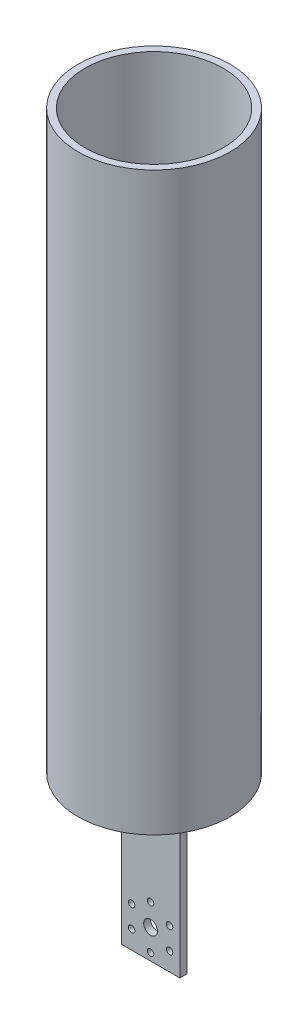
SolidWorks part; units mm, degrees
material "1060 Alloy"
ref_plane "Front Plane" through (0, 0, 0) normal (0, 0, 1) x (1, 0, 0)
ref_plane "Top Plane" through (0, 0, 0) normal (0, 1, 0) x (1, 0, 0)
ref_plane "Right Plane" through (0, 0, 0) normal (1, 0, 0) x (0, 0, -1)
sketch "Sketch1" plane through (0, 0, 0) normal (1, 0, 0) x (0, 0, -1)
  line L0 (0, 0) -> (3, 0)
  line L1 (3, 0) -> (3, 70)
  line L2 (3, 70) -> (0, 70)
  line L3 (0, 70) -> (0, 0)
  dimension "D1" = 3
  dimension "D2" = 70
  dimension "D3" = 3
extrude "Boss-Extrude1" add sketch "Sketch1" along normal blind 25.4
sketch "Sketch2" plane through (0, 0, 0) normal (0, 0, 1) x (1, 0, 0)
  line L0 (12.7, 0) -> (12.7, 12.7) construction
  line L1 (25.4, 0) -> (0, 0) construction
  circle A0 centre (12.7, 12.7) radius 3
  circle A2 centre (12.7, 22.2) radius 1.4
  circle A3 centre (20.9272, 17.45) radius 1.4
  circle A4 centre (20.9272, 7.95) radius 1.4
  circle A5 centre (12.7, 3.2) radius 1.4
  circle A6 centre (4.4728, 7.95) radius 1.4
  circle A7 centre (4.4728, 17.45) radius 1.4
  point P21 (12.7, 12.7)
  dimension "D2" = 6
  dimension "D4" = 2.8
  dimension "D1" = 12.7
  dimension "D5" = 6
extrude "Cut-Extrude1" cut sketch "Sketch2" against normal blind 25.4
sketch "Sketch3" plane through (0, 70, 0) normal (0, 1, 0) x (1, 0, 0)
  line L0 (12.7, 0) -> (42.7, 0) construction
  line L1 (25.4, 0) -> (0, 0) construction
  line L2 (12.7, 0) -> (42.7, 0)
  line L3 (42.7, 0) -> (42.7, 3)
  line L4 (42.7, 3) -> (-17.3, 3)
  line L5 (-17.3, 3) -> (-17.3, 0)
  line L6 (-17.3, 0) -> (12.7, 0)
  dimension "D1" = 30
  dimension "D2" = 3
  dimension "D3" = 60
extrude "Boss-Extrude2" add sketch "Sketch3" along normal blind 100
sketch "Sketch4" plane through (0, 70, 0) normal (0, -1, 0) x (1, 0, 0)
  line L0 (-17.3, -1.5) -> (42.7, -1.5) construction
  line L1 (-17.3, -3) -> (-17.3, 0) construction
  line L2 (42.7, 0) -> (42.7, -3) construction
  circle A0 centre (12.7, -1.5) radius 30
  circle A1 centre (12.7, -1.5) radius 33
  dimension "D1" = 60
  dimension "D2" = 66
extrude "Boss-Extrude3" add sketch "Sketch4" against normal blind 250
